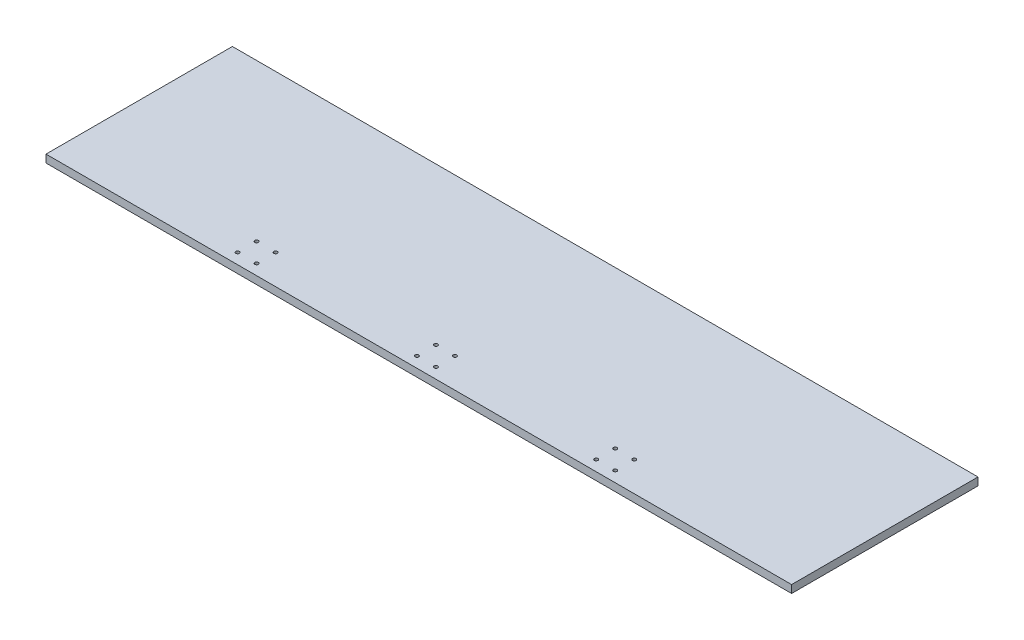
SolidWorks part; units mm, degrees
ref_plane "Front" through (0, 0, 0) normal (0, 0, 1) x (1, 0, 0)
ref_plane "Top" through (0, 0, 0) normal (0, 1, 0) x (1, 0, 0)
ref_plane "Right" through (0, 0, 0) normal (1, 0, 0) x (0, 0, -1)
sketch "Sketch1" plane through (0, 0, 0) normal (0, 1, 0) x (1, 0, 0)
  line L1 (-304.8, 76.2) -> (304.8, 76.2)
  line L2 (-304.8, 76.2) -> (-304.8, -76.2)
  line L3 (-304.8, -76.2) -> (304.8, -76.2)
  line L4 (304.8, 76.2) -> (304.8, -76.2)
  line L5 (-304.8, 76.2) -> (304.8, -76.2) construction
  line L6 (-304.8, -76.2) -> (304.8, 76.2) construction
  point P0 (0, 0)
  dimension "D1" = 609.6
  dimension "D2" = 152.4
extrude "Boss-Extrude1" add sketch "Sketch1" along normal blind 6.35
hole_wizard "M2.5 Clearance Hole1" positions "Sketch5" profile "Sketch6" hole size "M2.5" standard "ANSI Metric" end condition through all
sketch "Sketch5" plane through (0, 0, 0) normal (0, -1, 0) x (-1, 0, 0)
  point P0 (156.8782, -51.9218)
  point P3 (141.3218, -51.9218)
  point P6 (141.3218, -67.4782)
  point P9 (156.8782, -67.4782)
  point P12 (10.2782, -51.9218)
  point P15 (10.2782, -67.4782)
  point P18 (-5.2782, -67.4782)
  point P21 (-5.2782, -51.9218)
  point P24 (-136.3218, -51.9218)
  point P27 (-136.3218, -67.4782)
  point P30 (-151.8782, -67.4782)
  point P33 (-151.8782, -51.9218)
sketch "Sketch6" plane through (-156.8782, 0, 51.9218) normal (1, 0, 0) x (0, 0, -1)
  line L0 (0, 0) -> (0, 6.35)
  line L1 (0, 6.35) -> (1.45, 6.35)
  line L2 (1.45, 6.35) -> (1.45, 0)
  line L5 (1.45, 0) -> (0, 0)
  line L11 (0, -6.35) -> (0, 107.95) construction
  dimension "Thru Hole Dia." = 2.9
  dimension "Thru Hole Depth" = 6.35
